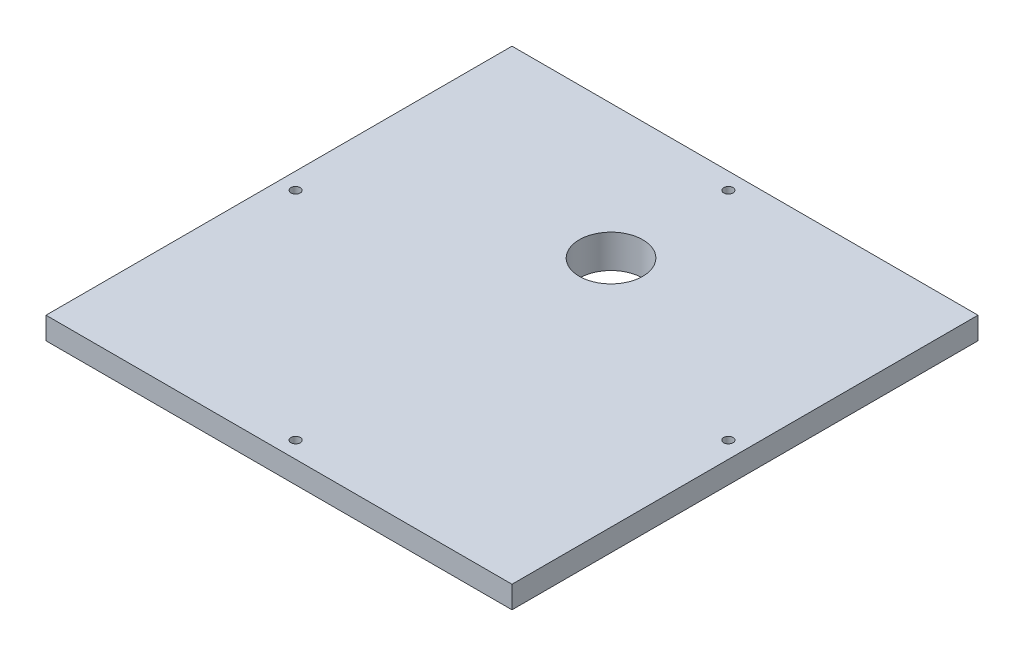
SolidWorks part; units mm, degrees
ref_plane "Front Plane" through (0, 0, 0) normal (0, 0, 1) x (1, 0, 0)
ref_plane "Top Plane" through (0, 0, 0) normal (0, 1, 0) x (1, 0, 0)
ref_plane "Right Plane" through (0, 0, 0) normal (1, 0, 0) x (0, 0, -1)
sketch "Sketch2" plane through (0, 0, 0) normal (0, 1, 0) x (1, 0, 0)
  line L1 (-105, -105) -> (105, -105)
  line L2 (-105, -105) -> (-105, 105)
  line L3 (-105, 105) -> (105, 105)
  line L4 (105, -105) -> (105, 105)
  line L5 (-105, -105) -> (105, 105) construction
  line L6 (-105, 105) -> (105, -105) construction
  point P0 (0, 0)
  dimension "D1" = 210
  dimension "D2" = 210
extrude "Boss-Extrude1" add sketch "Sketch2" along normal blind 10
sketch "Sketch3" plane through (0, 0, 0) normal (0, -1, 0) x (1, 0, 0)
  line L1 (-89.8, -89.8) -> (89.8, -89.8)
  line L2 (-89.8, -89.8) -> (-89.8, 89.8)
  line L3 (-89.8, 89.8) -> (89.8, 89.8)
  line L4 (89.8, -89.8) -> (89.8, 89.8)
  line L5 (-89.8, -89.8) -> (89.8, 89.8) construction
  line L6 (-89.8, 89.8) -> (89.8, -89.8) construction
  point P0 (0, 0)
  dimension "D1" = 179.6
  dimension "D2" = 179.6
extrude "Boss-Extrude2" add sketch "Sketch3" along normal blind 5 draft 2
sketch "Sketch4" plane through (0, 10, 0) normal (0, 1, 0) x (1, 0, 0)
  line L0 (-89.6254, 89.6254) -> (89.6254, 89.6254) construction
  circle A0 centre (0, 44.6254) radius 14.3
  dimension "D1" = 28.6
  dimension "D2" = 45
extrude "Cut-Extrude1" cut sketch "Sketch4" against normal up to surface (15 mm away) up to face at (0, -5, 0)
sketch "Sketch6" plane through (0, 10, 0) normal (0, 1, 0) x (1, 0, 0)
  line L0 (105, 105) -> (-105, 105) construction
  line L1 (-1000, 0) -> (49000, 0) construction
  line L2 (0, -1000) -> (0, 49000) construction
  line L3 (-105, 105) -> (-105, -105) construction
  circle A0 centre (0, 97.5) radius 2.1
  circle A1 centre (0, 97.5) radius 2.1
  circle A2 centre (0, 97.5) radius 2.1
  circle A3 centre (0, 97.5) radius 2.1
  circle A4 centre (0, -97.5) radius 2.1
  circle A5 centre (-97.5, 0) radius 2.1
  circle A6 centre (97.5, 0) radius 2.1
  dimension "D1" = 4.2
  dimension "D4" = 4.2
  dimension "D2" = 7.5
  dimension "D3" = 4
  dimension "D5" = 7.5
extrude "Cut-Extrude2" cut sketch "Sketch6" against normal up to surface (10 mm away) contours A2 | A5 | A4 | A6 | A0 | A1 | A3 up to face at (0, 0, 0)
fillet "Fillet1" radius 5 4 edges at (89.7127, -2.5, 89.7127) (89.7127, -2.5, -89.7127) (-89.7127, -2.5, -89.7127) (-89.7127, -2.5, 89.7127)
